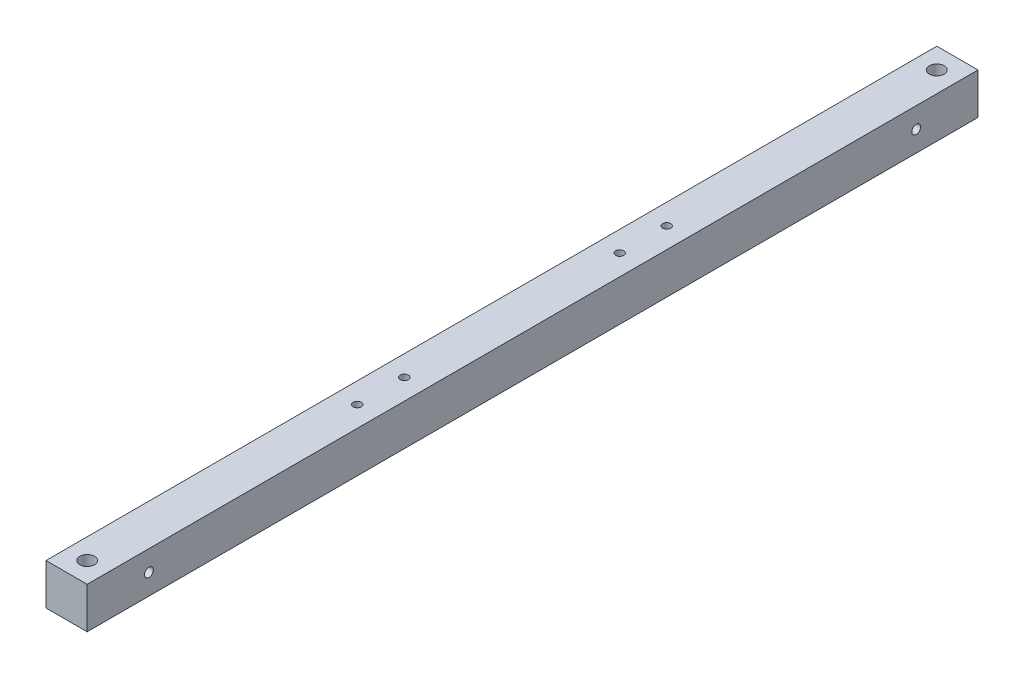
SolidWorks part; units mm, degrees
ref_plane "Ön Düzlem" through (0, 0, 0) normal (0, 0, 1) x (1, 0, 0)
ref_plane "Üst Düzlem" through (0, 0, 0) normal (0, 1, 0) x (1, 0, 0)
ref_plane "Sağ Düzlem" through (0, 0, 0) normal (1, 0, 0) x (0, 0, -1)
sketch "Çizim1" plane through (0, 0, 0) normal (0, 0, 1) x (1, 0, 0)
  line L1 (-14, -14) -> (14, -14)
  line L2 (-14, -14) -> (-14, 14)
  line L3 (-14, 14) -> (14, 14)
  line L4 (14, -14) -> (14, 14)
  line L5 (-14, -14) -> (14, 14) construction
  line L6 (-14, 14) -> (14, -14) construction
  point P0 (0, 0)
  dimension "D1" = 28
  dimension "D2" = 28
extrude "Yükseklik-Ekstrüzyon1" add sketch "Çizim1" along normal blind 606
sketch "Çizim2" plane through (14, 0, 0) normal (1, 0, 0) x (0, 0, -1)
  line L0 (-606, 14) -> (0, 14) construction
  line L1 (0, -14) -> (0, 14) construction
  line L2 (-606, -14) -> (-606, 14) construction
  circle A0 centre (-42, 0) radius 3
  circle A1 centre (-564, 0) radius 3
  dimension "D1" = 14
  dimension "D2" = 6
  dimension "D3" = 6
  dimension "D5" = 42
  dimension "D4" = 42
  dimension "D6" = 14
extrude "Kes-Ekstrüzyon1" cut sketch "Çizim2" against normal blind 40
sketch "Çizim4" plane through (-14, 0, 0) normal (-1, 0, 0) x (0, 0, 1)
  circle A0 centre (42, 0) radius 5
  circle A1 centre (564, 0) radius 5
  dimension "D1" = 10
extrude "Kes-Ekstrüzyon2" cut sketch "Çizim4" against normal blind 7
sketch "Çizim5" plane through (0, 14, 0) normal (0, 1, 0) x (1, 0, 0)
  line L1 (14, 0) -> (-14, 0) construction
  line L2 (14, -606) -> (-14, -606) construction
  circle A0 centre (0, -592) radius 3
  circle A1 centre (0, -14) radius 3
  dimension "D1" = 6
  dimension "D2" = 14
  dimension "D3" = 14
extrude "Kes-Ekstrüzyon3" cut sketch "Çizim5" against normal through all and the other way through all
sketch "Çizim6" plane through (0, 14, 0) normal (0, 1, 0) x (1, 0, 0)
  circle A0 centre (0, -14) radius 5
  circle A1 centre (0, -592) radius 5
  dimension "D1" = 10
extrude "Kes-Ekstrüzyon4" cut sketch "Çizim6" against normal blind 7
sketch "Çizim8" plane through (0, 14, 0) normal (0, 1, 0) x (1, 0, 0)
  line L0 (-14, -303) -> (14, -303) construction
  line L1 (-14, -606) -> (-14, 0) construction
  line L2 (14, -606) -> (14, 0) construction
  line L3 (-14, -606) -> (-14, 0) construction
  line L4 (0, -408.25) -> (0, -376.25) construction
  circle A0 centre (0, -408.25) radius 2.75
  circle A1 centre (0, -376.25) radius 2.75
  circle A2 centre (0, -229.75) radius 2.75
  circle A3 centre (0, -197.75) radius 2.75
  point P7 (-14, -303)
  point P11 (0, -392.25)
  point P13 (0, -303)
  dimension "D1" = 5.5
  dimension "D2" = 32
  dimension "D3" = 89.25
extrude "Kes-Ekstrüzyon6" cut sketch "Çizim8" against normal through all
